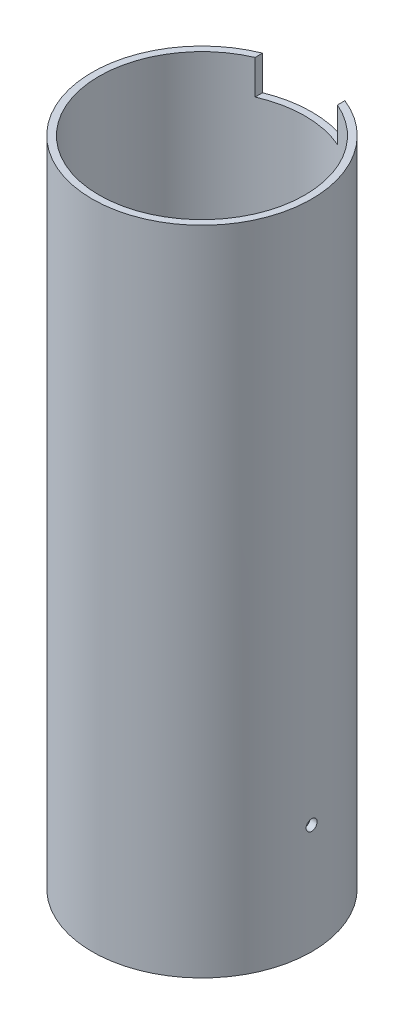
SolidWorks part; units mm, degrees
material "Acrylic (Medium-high impact)"
ref_plane "Front Plane" through (0, 0, 0) normal (0, 0, 1) x (1, 0, 0)
ref_plane "Top Plane" through (0, 0, 0) normal (0, 1, 0) x (1, 0, 0)
ref_plane "Right Plane" through (0, 0, 0) normal (1, 0, 0) x (0, 0, -1)
sketch "Sketch1" plane through (0, 0, 0) normal (0, 1, 0) x (1, 0, 0)
  circle A0 centre (0, 0) radius 47.625
  dimension "D1" = 95.25
extrude "Extrude-Thin1" add sketch "Sketch1" along normal blind 301.625 thin
sketch "Sketch2" plane through (0, 0, 0) normal (0, 0, 1) x (1, 0, 0)
  line L0 (50.8, 301.625) -> (-50.8, 301.625) construction
  line L1 (-19.05, 317.5) -> (19.05, 317.5)
  line L2 (-19.05, 317.5) -> (-19.05, 285.75)
  line L3 (-19.05, 285.75) -> (19.05, 285.75)
  line L4 (19.05, 317.5) -> (19.05, 285.75)
  line L5 (-19.05, 317.5) -> (19.05, 285.75) construction
  line L6 (-19.05, 285.75) -> (19.05, 317.5) construction
  point P0 (0, 301.625)
  dimension "D1" = 38.1
  dimension "D2" = 15.875
extrude "Cut-Extrude1" cut sketch "Sketch2" against normal up to surface (47.0929 mm away)
sketch "Sketch3" plane through (0, 0, 0) normal (1, 0, 0) x (0, 0, -1)
  line L0 (-50.8, 0) -> (50.8, 0) construction
  circle A0 centre (0, 50.8) radius 2.54
  dimension "D1" = 5.08
  dimension "D2" = 50.8
extrude "Cut-Extrude2" cut sketch "Sketch3" against normal up to surface and the other way up to surface up to face at (0, 293.6875, -23.5464) other way up to face at (0, 293.6875, -23.5464)
sketch "Sketch4" plane through (0, 0, 0) normal (1, 0, 0) x (0, 0, -1)
  line L0 (-50.8, 0) -> (50.8, 0) construction
  circle A0 centre (0, 203.2) radius 2.54
  dimension "D2" = 5.08
  dimension "D1" = 203.2
extrude "Cut-Extrude3" cut sketch "Sketch4" against normal up to surface (50.7365 mm away)
